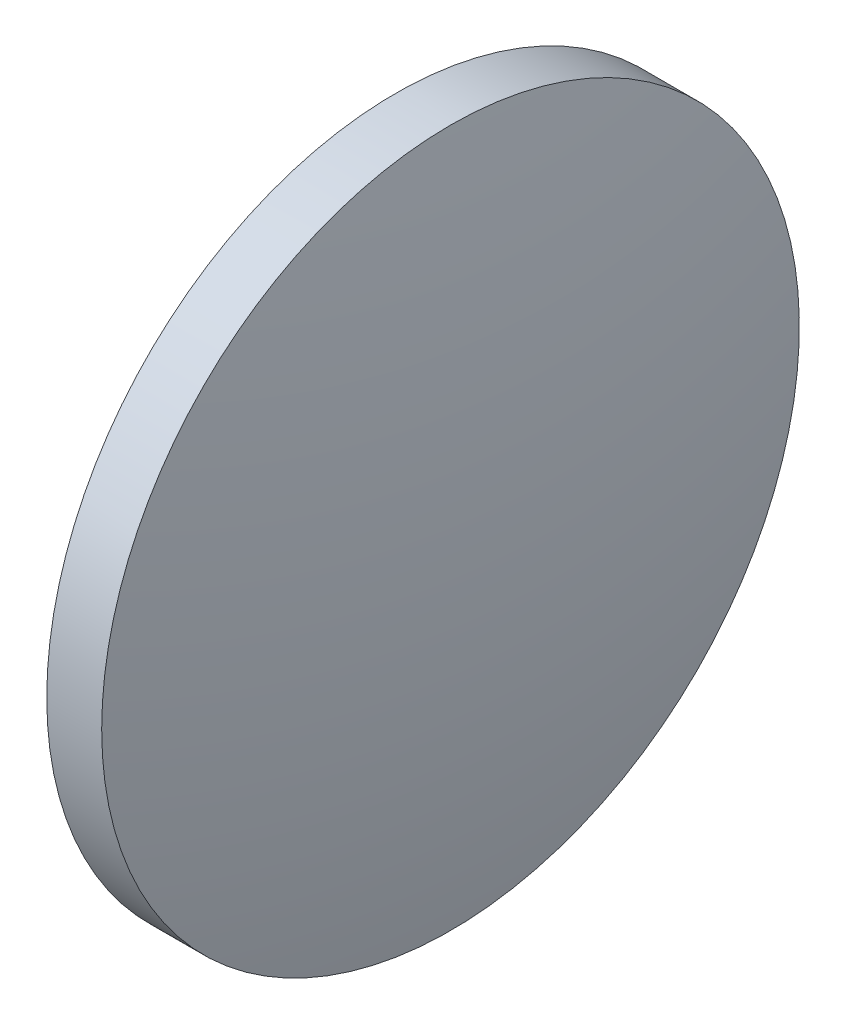
SolidWorks part; units mm, degrees
ref_plane "前视基准面" through (0, 0, 0) normal (0, 0, 1) x (1, 0, 0)
ref_plane "上视基准面" through (0, 0, 0) normal (0, 1, 0) x (1, 0, 0)
ref_plane "右视基准面" through (0, 0, 0) normal (1, 0, 0) x (0, 0, -1)
sketch "草图1" plane through (0, 0, 0) normal (0, 0, 1) x (1, 0, 0)
  line L0 (384.2382, 40.4417) -> (403.0341, 40.4417) construction
  line L1 (389.868, 40.4417) -> (389.868, 53.1417)
  line L2 (389.868, 53.1417) -> (391.868, 53.1417)
  line L3 (393.168, 40.4417) -> (389.868, 40.4417)
  arc A0 (393.168, 40.4417) -> (391.868, 53.1417) centre (330.4834, 40.4417) ccw
revolve "旋转1" add sketch "草图1" angle 360 about L0
